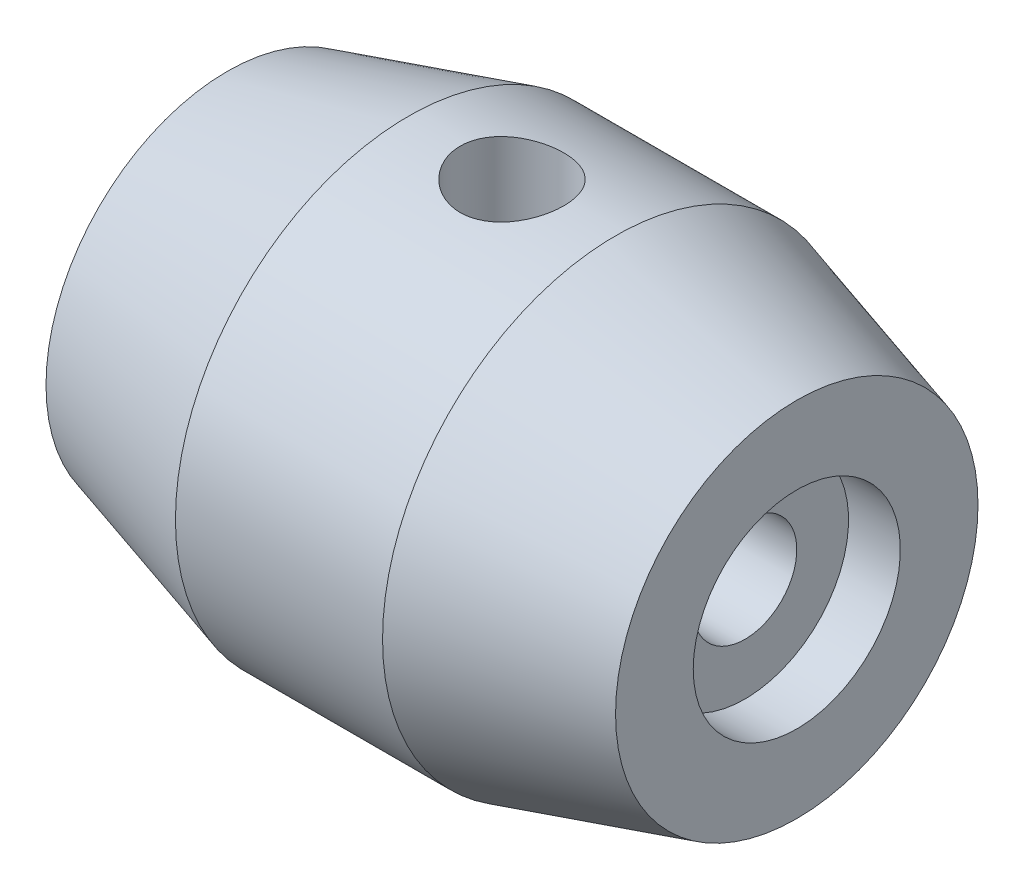
SolidWorks part; units mm, degrees
ref_plane "Front Plane" through (0, 0, 0) normal (0, 0, 1) x (1, 0, 0)
ref_plane "Top Plane" through (0, 0, 0) normal (0, 1, 0) x (1, 0, 0)
ref_plane "Right Plane" through (0, 0, 0) normal (1, 0, 0) x (0, 0, -1)
sketch "Sketch1" plane through (0, 0, 0) normal (0, 1, 0) x (1, 0, 0)
  line L0 (0, 0) -> (4.5, 0)
  line L1 (4.5, 0) -> (4.5, 0.5)
  line L2 (4.5, 0.5) -> (5, 0.5)
  line L3 (5, 0.5) -> (5, 1.25)
  line L4 (5, 1.25) -> (3.25, 1.75)
  line L5 (3.25, 1.75) -> (1.25, 1.75)
  line L6 (1.25, 1.75) -> (-0.5, 1.25)
  line L7 (-0.5, 1.25) -> (-0.5, 0.5)
  line L8 (-0.5, 0.5) -> (0, 0.5)
  line L9 (0, 0.5) -> (0, 0)
  line L10 (0, -0.5) -> (4.5, -0.5)
  line L11 (0, 0) -> (0, -0.5) construction
  dimension "D1" = 0.5
  dimension "D2" = 0.75
  dimension "D3" = 1.75
  dimension "D4" = 5.5
  dimension "D5" = 1.75
  dimension "D6" = 1.75
  dimension "D7" = 0.5
revolve "Revolve1" add sketch "Sketch1" angle 360 about L10
ref_plane "Plane2" through (0, 2, 0) normal (0, 1, 0) x (1, 0, 0)
sketch "Sketch3" plane through (0, 2, 0) normal (0, 1, 0) x (1, 0, 0)
  line L0 (-0.5, -0.5) -> (5, -0.5) construction
  line L1 (-0.5, 1.25) -> (-0.5, -2.25) construction
  line L2 (5, -2.25) -> (5, 1.25) construction
  line L3 (2.25, 1.75) -> (2.25, -1.7455) construction
  line L4 (3.25, 1.75) -> (1.25, 1.75) construction
  circle A0 centre (2.25, -0.5) radius 0.5
  dimension "D1" = 1
extrude "Cut-Extrude2" cut sketch "Sketch3" against normal through all both and the other way through all
